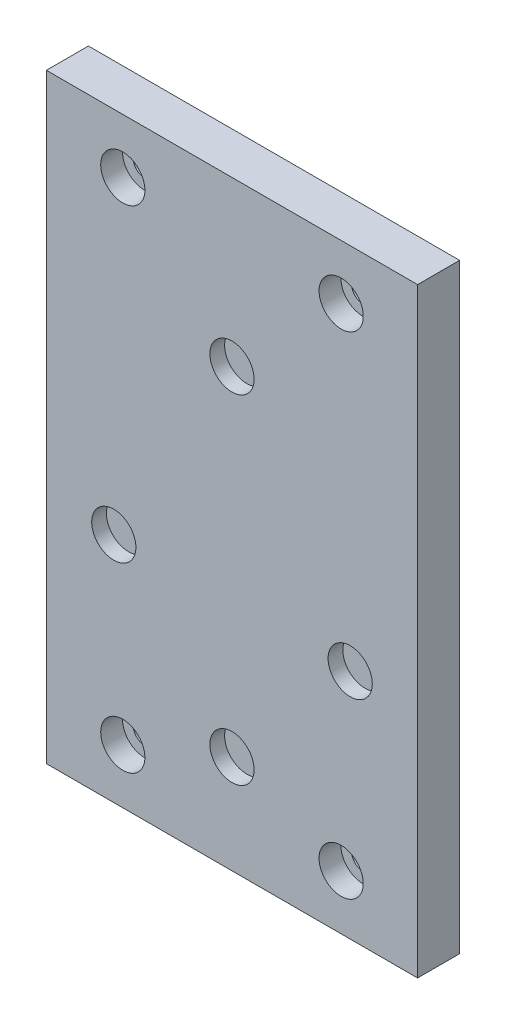
SolidWorks part; units mm, degrees
ref_plane "Front Plane" through (0, 0, 0) normal (0, 0, 1) x (1, 0, 0)
ref_plane "Top Plane" through (0, 0, 0) normal (0, 1, 0) x (1, 0, 0)
ref_plane "Right Plane" through (0, 0, 0) normal (1, 0, 0) x (0, 0, -1)
sketch "Sketch1" plane through (0, 0, 0) normal (0, 0, 1) x (1, 0, 0)
  line L0 (0, -45) -> (0, -41) construction
  line L1 (-34, 55) -> (34, 55)
  line L2 (-34, 55) -> (-34, -55)
  line L3 (-34, -55) -> (34, -55)
  line L4 (34, 55) -> (34, -55)
  line L5 (-34, 55) -> (34, -55) construction
  line L6 (-34, -55) -> (34, 55) construction
  line L7 (-20, 45) -> (20, 45) construction
  line L8 (-20, 45) -> (-20, -45) construction
  line L9 (-20, -45) -> (20, -45) construction
  line L10 (20, 45) -> (20, -45) construction
  line L11 (-20, 45) -> (20, -45) construction
  line L12 (-20, -45) -> (20, 45) construction
  line L13 (0, 25) -> (-21.6506, -12.5) construction
  line L14 (-21.6506, -12.5) -> (21.6506, -12.5) construction
  line L15 (21.6506, -12.5) -> (0, 25) construction
  circle A0 centre (20, 45) radius 2.1
  circle A1 centre (-20, 45) radius 2.1
  circle A2 centre (20, -45) radius 2.1
  circle A3 centre (-20, -45) radius 2.1
  circle A4 centre (0, 0) radius 25 construction
  circle A5 centre (21.6506, -12.5) radius 4.05
  circle A6 centre (0, 25) radius 4.05
  circle A7 centre (-21.6506, -12.5) radius 4.05
  circle A9 centre (0, -36.95) radius 4.05
  point P0 (0, 0)
  point P6 (0, 0)
extrude "Boss-Extrude1" add sketch "Sketch1" along normal blind 7.7
sketch "Sketch2" plane through (0, 0, 0) normal (0, 0, -1) x (-1, 0, 0)
  circle A0 centre (-21.6506, -12.5) radius 6.3046
  circle A1 centre (0, 25) radius 7.3343
  circle A2 centre (21.6506, -12.5) radius 8.114
  circle A3 centre (0, -36.95) radius 11.0737
extrude "Boss-Extrude2" add sketch "Sketch2" against normal blind 5
sketch "Sketch3" plane through (0, 0, 7.7) normal (0, 0, -1) x (-1, 0, 0)
  circle A0 centre (-20, 45) radius 4.05
  circle A1 centre (20, 45) radius 4.05
  circle A2 centre (-20, -45) radius 4.05
  circle A3 centre (20, -45) radius 4.05
extrude "Cut-Extrude1" cut sketch "Sketch3" along normal blind 4
